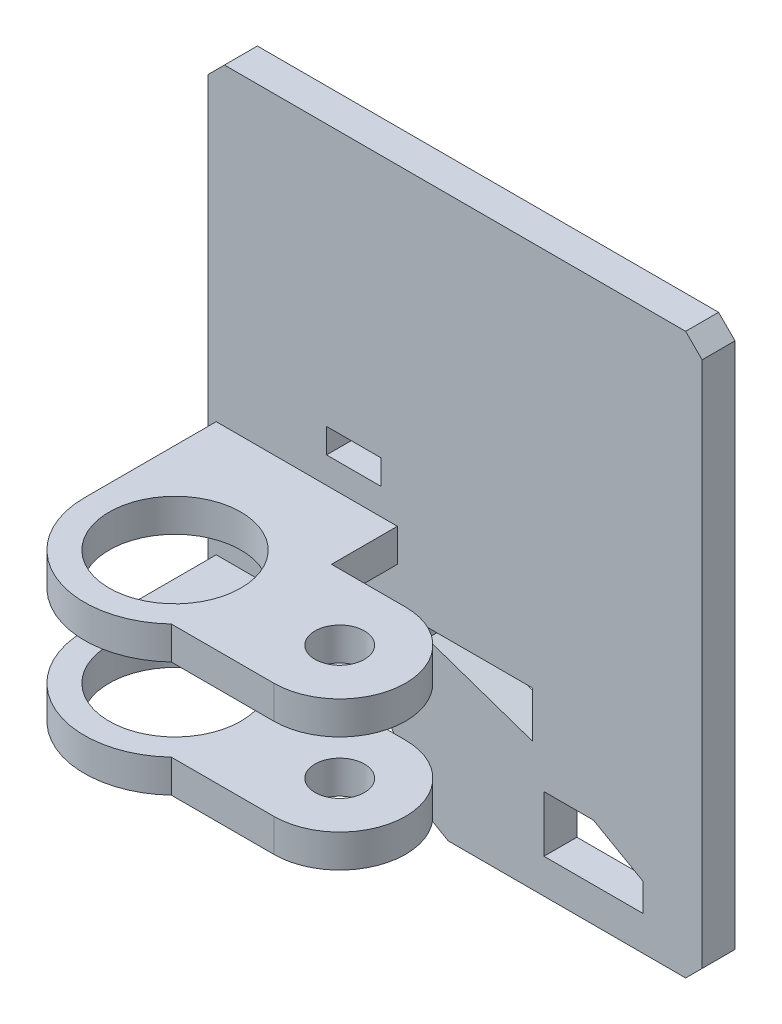
SolidWorks part; units mm, degrees
material "Plain Carbon Steel"
ref_plane "Front" through (0, 0, 0) normal (0, 0, 1) x (1, 0, 0)
ref_plane "Top" through (0, 0, 0) normal (0, 1, 0) x (1, 0, 0)
ref_plane "Right" through (0, 0, 0) normal (1, 0, 0) x (0, 0, -1)
sketch "Sketch2" plane through (0, 0, 0) normal (0, 0, 1) x (1, 0, 0)
  line L0 (-140, -110) -> (-48.7821, -110)
  line L1 (140, 170) -> (-140, 170)
  line L2 (150, 160) -> (150, -160)
  line L3 (140, -170) -> (-4.1411, -170)
  line L4 (-150, 160) -> (-150, -100)
  line L5 (150, 170) -> (-97.0588, -110) construction
  line L6 (150, -170) -> (-150, 170) construction
  line L7 (-48.7821, -110) -> (-19.1411, -161.3397)
  line L8 (84, -115) -> (114, -132)
  line L9 (54, -149) -> (114, -149)
  line L10 (54, -149) -> (54, -115)
  line L11 (54, -115) -> (84, -115)
  line L12 (114, -149) -> (114, -132)
  line L13 (-140, 170) -> (-150, 160)
  line L14 (150, 160) -> (140, 170)
  line L15 (47, -92) -> (-17, -70)
  line L16 (-17, -64) -> (47, -64)
  line L17 (-17, -64) -> (-17, -70)
  line L19 (47, -64) -> (47, -92)
  line L20 (-17, -64) -> (47, -92) construction
  line L21 (150, -160) -> (140, -170)
  line L22 (-78, 11) -> (-45, 11)
  line L23 (-78, 11) -> (-78, -4)
  line L24 (-78, -4) -> (-45, -4)
  line L25 (-45, 11) -> (-45, -4)
  line L26 (-78, 11) -> (-45, -4) construction
  line L27 (-78, -4) -> (-45, 11) construction
  line L28 (-19.1411, -161.3397) -> (-4.1411, -170)
  line L29 (-150, -100) -> (-140, -110)
  point P0 (0, 0)
  point P6 (-150, -110)
  point P8 (-14.1411, -170)
  point P21 (-61.5, 3.5)
  dimension "D1" = 300
  dimension "D2" = 340
  dimension "D3" = 280
  dimension "D4" = 240
  dimension "D5" = 150
  dimension "D6" = 135.8589
  dimension "D7" = 21
  dimension "D8" = 34
  dimension "D9" = 23
  dimension "D10" = 22
  dimension "D11" = 6
  dimension "D12" = 60
  dimension "D13" = 15
  dimension "D14" = 36
  dimension "D15" = 30
  dimension "D16" = 30
  dimension "D17" = 17
  dimension "D18" = 103
  dimension "D19" = 64
  dimension "D20" = 33
  dimension "D21" = 195
extrude "Boss-Extrude1" add sketch "Sketch2" along normal blind 20
sketch "Sketch7" plane through (0, -110, 0) normal (0, -1, 0) x (1, 0, 0)
  line L0 (-145, 20) -> (-145, 100)
  line L1 (-140, 20) -> (-48.7821, 20) construction
  line L2 (-35, 20) -> (-35, 60)
  line L3 (-150, 20) -> (-150, 0) construction
  line L4 (-145, 20) -> (-35, 20)
  line L5 (-35, 60) -> (10, 60)
  line L6 (10, 140) -> (-52.2508, 140)
  circle A0 centre (-90, 100) radius 40
  arc A1 (-52.2508, 140) -> (-145, 100) centre (-90, 100) ccw
  circle A2 centre (10, 100) radius 15
  arc A3 (10, 60) -> (10, 140) centre (10, 100) ccw
  dimension "D3" = 80
  dimension "D7" = 30
  dimension "D8" = 80
  dimension "D1" = 5
  dimension "D2" = 110
  dimension "D4" = 80
  dimension "D5" = 55
  dimension "D6" = 100
  dimension "D9" = 40
extrude "Boss-Extrude5" add sketch "Sketch7" against normal blind 20
pattern_linear "LPattern2" count 2 spacing 70 along (0, 1, 0) of "Boss-Extrude5"
